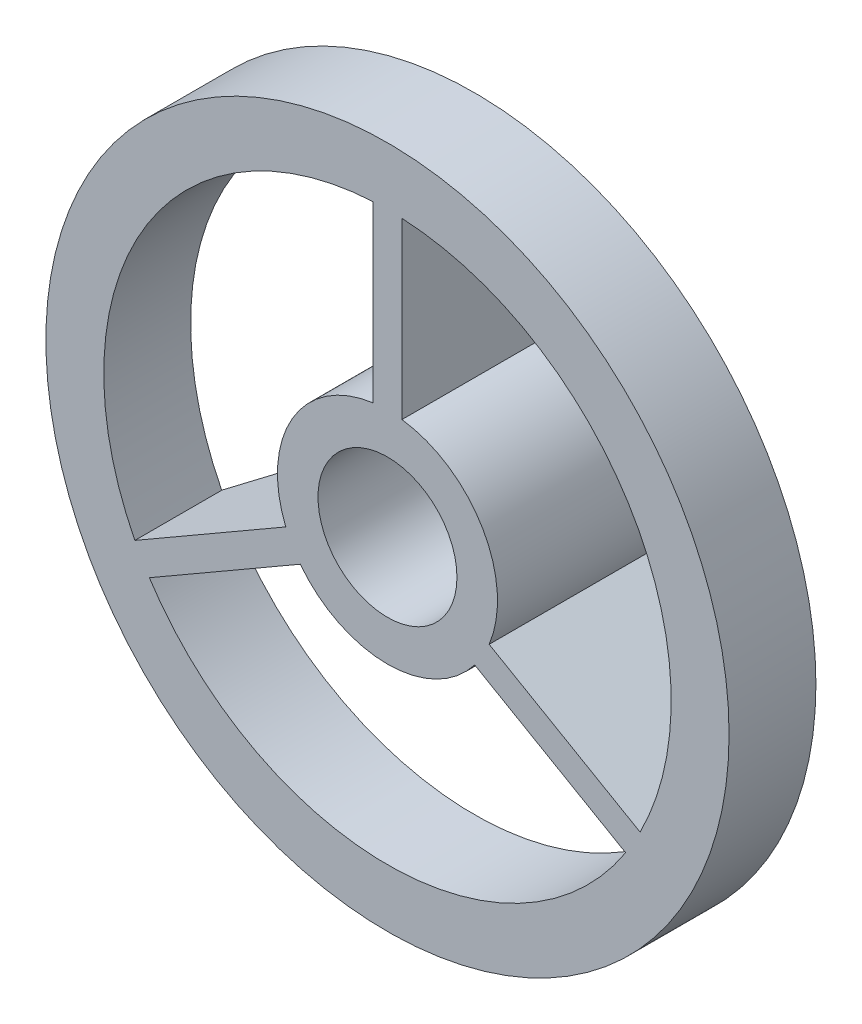
SolidWorks part; units mm, degrees
material "ABS"
ref_plane "Front Plane" through (0, 0, 0) normal (0, 0, 1) x (1, 0, 0)
ref_plane "Top Plane" through (0, 0, 0) normal (0, 1, 0) x (1, 0, 0)
ref_plane "Right Plane" through (0, 0, 0) normal (1, 0, 0) x (0, 0, -1)
sketch "Sketch1" plane through (0, 0, 0) normal (0, 0, 1) x (1, 0, 0)
  circle A0 centre (0, 0) radius 1.2
  circle A1 centre (0, 0) radius 1.9
  dimension "D1" = 2.4
  dimension "D2" = 0.7
extrude "Boss-Extrude1" add sketch "Sketch1" along normal blind 3.5
sketch "Sketch2" plane through (0, 0, 3.5) normal (0, 0, 1) x (1, 0, 0)
  circle A1 centre (0, 0) radius 5.9
  circle A2 centre (0, 0) radius 4.9
  circle A3 centre (0, 0) radius 4.9
  dimension "D1" = 3
  dimension "D2" = 1
extrude "Boss-Extrude2" add sketch "Sketch2" against normal blind 1.5 separate body
sketch "Sketch3" plane through (0, 0, 0) normal (1, 0, 0) x (0, 0, -1)
  line L0 (-3.5, 1.9) -> (0, 1.9) construction
  line L1 (-3.5, 1.9) -> (-3.5, -1.9) construction
  line L2 (-3.5, 4.9) -> (-3.5, -4.9) construction
  line L3 (0, -1.9) -> (0, 1.9) construction
  line L4 (0, 1.9) -> (-2, 4.9)
  line L5 (-2, -4.9) -> (-2, 4.9) construction
  line L6 (-2, -5.9) -> (-2, 5.9) construction
  line L7 (-2, 4.9) -> (-3.5, 4.9)
  line L8 (-3.5, 4.9) -> (-3.5, 1.9)
  line L9 (-3.5, 1.7) -> (0, 1.7)
  line L10 (-3.5, 1.9) -> (-3.5, 1.7)
  line L11 (0, 1.9) -> (0, 1.7)
  line L12 (0, 1.9) -> (0, 1.7)
  dimension "D1" = 0.2
extrude "Boss-Extrude3" add sketch "Sketch3" along normal mid plane 0.5 contours L8 L0 L4 L7 | L0 L10 L9 L11
pattern_circular "CirPattern1" count 3 over 360 about axis through (0, 0, 0) along (0, 0, 1) of "Boss-Extrude3"
